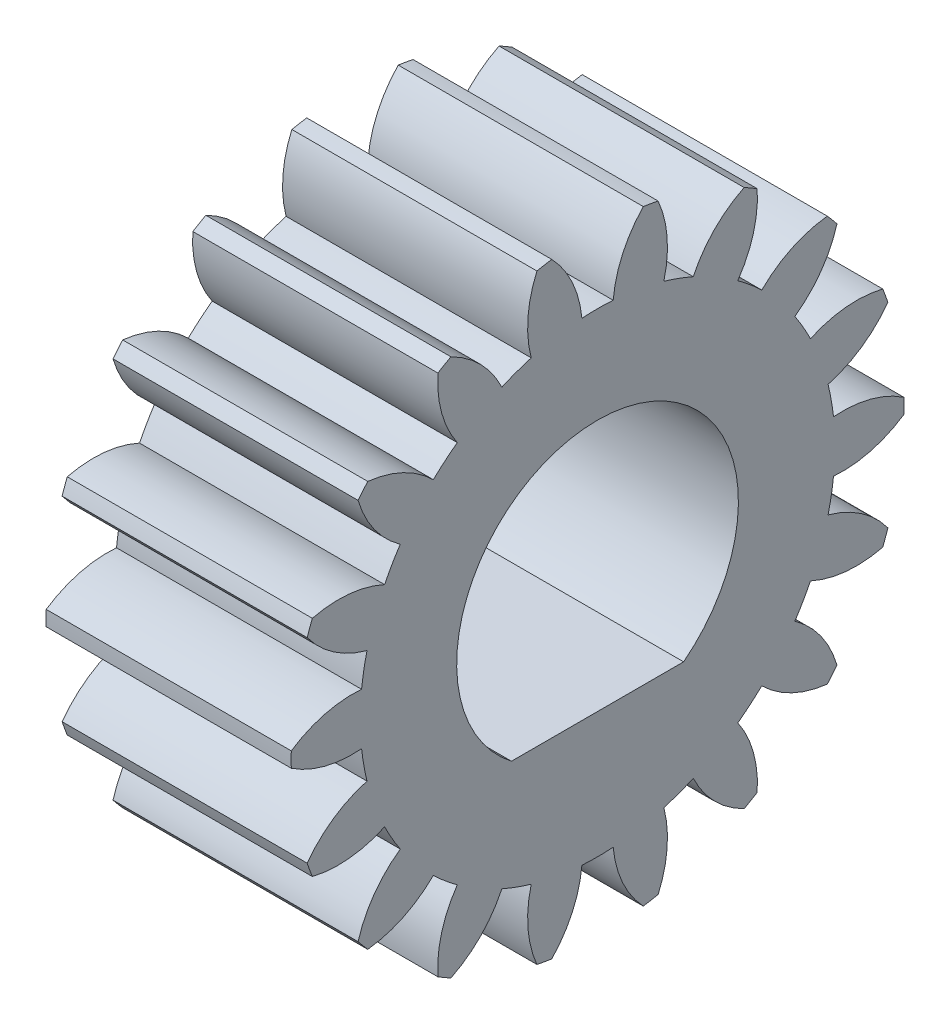
SolidWorks part; units mm, degrees
ref_plane "Plane1" through (0, 0, 0) normal (0, 0, 1) x (1, 0, 0)
ref_plane "Plane2" through (0, 0, 0) normal (0, 1, 0) x (1, 0, 0)
ref_plane "Plane3" through (0, 0, 0) normal (1, 0, 0) x (0, 0, -1)
sketch "HoldingSke" plane through (0, 0, 0) normal (0, 1, 0) x (1, 0, 0)
  line L0 (0, 0) -> (1.9021, -0.618)
  line L1 (-15, 0) -> (100, 0) construction
  line L2 (0, 0) -> (-2.1039, 2.3779)
  line L3 (0, 0) -> (-11.863, 4.5341)
  line L4 (0, 0) -> (8.2133, 2.6687)
  line L5 (0, 0) -> (-46.8476, -17.4728)
  line L6 (0, 0) -> (-3.3159, -2.2372)
  line L7 (-2.1039, 2.3779) -> (8.6586, 51.2059)
  line L8 (-76.2, 54.61) -> (-76.1, 54.61)
  line L9 (-71.009, 38.7566) -> (-53.1078, 45.2721)
  line L10 (-76.2, 71.12) -> (104.1128, 71.12)
  line L11 (0, 0) -> (-4, 0)
  line L12 (-76.2, 101.6) -> (-76.181, 101.6)
  line L13 (24.9733, 27.94) -> (52.9518, 28.4284)
  line L14 (24.9733, 27.94) -> (24.9743, 27.94)
  line L15 (24.9733, 27.94) -> (100.4006, 29.5858)
  line L16 (-63.627, -0.5) -> (-12.827, -0.5)
  circle A0 centre (0, 0) radius 0.5
  circle A1 centre (0, 0) radius 3.874
  circle A2 centre (0, 0) radius 37.5
  circle A3 centre (0, 0) radius 0.5
  dimension "MHD" = 7.748
  dimension "Hub_dia" = 75
  dimension "Bore" = 1
  dimension "MBD" = 1
  dimension "Num_teeth" = 18
  dimension "Pitch" = 2
  dimension "Overall_len" = 50
  dimension "Show_teeth" = 18
  dimension "Thickness" = 4
  dimension "OAL" = 50.0001
  dimension "T_dim" = 0.1
  dimension "Ap" = 20
  dimension "H" = 19.05
  dimension "Pitch_radius" = 180.3128
  dimension "Width" = 4
  dimension "Backlash" = 0.019
  dimension "Addendum_fac" = 1
  dimension "Dedendum_fac" = 1.25
  dimension "Clearance_fac" = 0.25
  dimension "Dedendum_add" = 0.001
  dimension "Module" = 0.5
sketch "BasProSke" plane through (0, 0, 0) normal (0, 1, 0) x (1, 0, 0)
  line L0 (-10, 0) -> (60, 0) construction
  line L1 (0, 0) -> (0, 5)
  line L2 (0, 0) -> (4, 0)
  line L3 (4, 0) -> (4, 5)
  line L4 (4, 5) -> (0, 5)
  dimension "Thickness" = 4
  dimension "Diameter" = 10
revolve "Base-Revolve" add sketch "BasProSke" angle 360 about L0
sketch "TooCutSke" plane through (0, 0, 0) normal (1, 0, 0) x (0, 0, -1)
  line L1 (0, 0) -> (0, 107) construction
  line L2 (0, 0) -> (-0.4254, 4.4798) construction
  line L3 (0, 0) -> (-1.5579, 8.835) construction
  line L4 (-0.4254, 4.4798) -> (-0.7789, 4.4175) construction
  arc A0 (0.2553, 3.8656) -> (-0.2553, 3.8656) centre (0, 0) ccw
  arc A1 (0.7686, 4.9663) -> (-0.7686, 4.9663) centre (0, 0) ccw
  circle A2 centre (0, 0) radius 4.5 construction
  circle A3 centre (0, 0) radius 4.2286 construction
  arc A4 (-0.2553, 3.8656) -> (-0.7686, 4.9663) centre (-2.0476, 3.6998) ccw
  arc A5 (0.7686, 4.9663) -> (0.2553, 3.8656) centre (2.0476, 3.6998) ccw
  dimension "Root_dia" = 7.748
  dimension "Overcut_dia" = 10.0508
  dimension "Pitch_dia" = 9
  dimension "Base_dia" = 8.4572
  dimension "Flank_rad" = 1.8
  dimension "Half_ang" = 10
  dimension "Half_CT" = 0.359
extrude "ToothCut" cut sketch "TooCutSke" along normal through all
fillet "Breaks" [suppressed] radius 0.01
fillet "RootFillets" [suppressed] radius 0.126
pattern_circular "TeethCuts" count 18 every 20 about axis through (-10, 0, 0) along (1, 0, 0) of "ToothCut", "RootFillets", "Breaks"
sketch "HubNeaOneSke" plane through (0, 0, 0) normal (-1, 0, 0) x (0, 0, 1)
  circle A0 centre (0, 0) radius 3.874
  dimension "Diameter" = 7.748
extrude "HubNearOne" [suppressed] add sketch "HubNeaOneSke" along normal blind 46.0001
sketch "HubNeaBotSke" plane through (0, 0, 0) normal (-1, 0, 0) x (0, 0, 1)
  circle A0 centre (0, 0) radius 3.874
  dimension "Diameter" = 7.748
extrude "HubNearBoth" [suppressed] add sketch "HubNeaBotSke" along normal blind 23
ref_plane "FarPln" through (4, 0, 0) normal (1, 0, 0) x (0, 0, -1)
sketch "HubFarSke" plane through (4, 0, 0) normal (1, 0, 0) x (0, 0, -1)
  circle A0 centre (0, 0) radius 3.874
  dimension "Diameter" = 7.748
extrude "HubFar" [suppressed] add sketch "HubFarSke" along normal blind 23
sketch "BorSke" plane through (0, 0, 0) normal (1, 0, 0) x (0, 0, -1)
  line L0 (-1.4048, -1.82) -> (1.4048, -1.82)
  line L2 (0, 0) -> (0, -1.82)
  arc A0 (-1.4048, -1.82) -> (1.4048, -1.82) centre (0, 0) cw
  point P2 (0, -1.5609)
extrude "Bore" cut sketch "BorSke" along normal mid plane 100.0001
sketch "KeySke" plane through (0, 0, 0) normal (1, 0, 0) x (0, 0, -1)
  line L0 (-0.05, 0) -> (-0.05, 0.6)
  line L1 (-0.05, 0.6) -> (0.05, 0.6)
  line L2 (0.05, 0.6) -> (0.05, 0)
  line L3 (0, 0) -> (0, 34) construction
  line L4 (-0.05, 0) -> (0.05, 0)
  dimension "Offset" = 0.6
  dimension "Width" = 0.1
extrude "Keyway" [suppressed] cut sketch "KeySke" along normal mid plane 100.0001
pattern_circular "Keyway2" [suppressed] count 2 every 90 about axis through (-10, 0, 0) along (1, 0, 0)
equation "' \"Module@HoldingSke\" = 6.35"
equation "' \"Num_teeth@HoldingSke\" = 12"
equation "' \"Ap@HoldingSke\" =  20"
equation "' \"Ap@HoldingSke\" = 20"
equation "' \"Width@HoldingSke\" = 0.5 * 25.4"
equation "' \"Hub_dia@HoldingSke\"= 1 * 25.4"
equation "' \"Hub_dia@HoldingSke\" = 1 * 25.4"
equation "' \"Overall_len@HoldingSke\" = 1.0 * 25.4"
equation "' \"Bore@HoldingSke\" = 0.75 * 25.4"
equation "' \"T_dim@HoldingSke\" = 0.1 * 25.4"
equation "' \"Width@KeySke\" = 0.25 * 25.4"
equation "' \"Show_teeth@HoldingSke\" = 13"
equation "' \"Backlash@HoldingSke\" = 0.009 * 25.4"
equation "' \"Addendum_fac@HoldingSke\" = 1.0"
equation "' \"Dedendum_fac@HoldingSke\" = 1.25"
equation "' \"Dedendum_add@HoldingSke\" = 0.00005 * 25.4"
equation "' \"Clearance_fac@HoldingSke\" = 0.25"
equation "\"Pitch@HoldingSke\" = 1 / \"Module@HoldingSke\""
equation "\"Overcut_dia@TooCutSke\" = (\"Num_teeth@HoldingSke\" + 2 * \"Addendum_fac@HoldingSke\") / \"Pitch@HoldingSke\" + 0.002 * 25.4"
equation "\"Pitch_dia@TooCutSke\" = \"Num_teeth@HoldingSke\" / \"Pitch@HoldingSke\""
equation "\"Base_dia@TooCutSke\" = \"Num_teeth@HoldingSke\" / \"Pitch@HoldingSke\" * cos((\"Ap@HoldingSke\"  * 3.14159265 / 180))"
equation "\"Root_dia@TooCutSke\" = (\"Num_teeth@HoldingSke\" + 2) / \"Pitch@HoldingSke\" - 2 * (\"Addendum_fac@HoldingSke\" + \"Dedendum_fac@HoldingSke\") / \"Pitch@HoldingSke\" - \"Dedendum_add@HoldingSke\" * 2"
equation "\"Half_ang@TooCutSke\" = 180 / \"Num_teeth@HoldingSke\""
equation "\"Half_CT@TooCutSke\" = \"Num_teeth@HoldingSke\" / \"Pitch@HoldingSke\" * sin((3.14159265 / 2 / \"Num_teeth@HoldingSke\")) / 2 - 7 * \"Backlash@HoldingSke\" / 4"
equation "\"Flank_rad@TooCutSke\" = \"Num_teeth@HoldingSke\" / \"Pitch@HoldingSke\" / 5"
equation "\"Radius@RootFillets\" = \"Clearance_fac@HoldingSke\" / \"Pitch@HoldingSke\" + \"Dedendum_add@HoldingSke\""
equation "\"Break_rad@Breaks\" = 0.02 / \"Pitch@HoldingSke\""
equation "\"Thickness@HoldingSke\" = \"Width@HoldingSke\""
equation "\"OAL@HoldingSke\" = \"Thickness@HoldingSke\""
equation "\"MHD@HoldingSke\" = (\"Num_teeth@HoldingSke\" + 2) / \"Pitch@HoldingSke\" - 2 * (\"Addendum_fac@HoldingSke\" + \"Dedendum_fac@HoldingSke\")  / \"Pitch@HoldingSke\" - \"Dedendum_add@HoldingSke\" * 2"
equation "\"MBD@HoldingSke\" = (\"Num_teeth@HoldingSke\" + 2) / \"Pitch@HoldingSke\" - 2 * (\"Addendum_fac@HoldingSke\" + \"Dedendum_fac@HoldingSke\")  / \"Pitch@HoldingSke\" - \"Dedendum_add@HoldingSke\" * 2 - 0.002 * 25.4"
equation "\"MHD@HoldingSke\" = ((sgn( \"MHD@HoldingSke\" - \"Hub_dia@HoldingSke\" )-1)*( \"MHD@HoldingSke\" - \"Hub_dia@HoldingSke\" ))/-2+ \"Hub_dia@HoldingSke\""
equation "\"MBD@HoldingSke\" = ((sgn( \"MBD@HoldingSke\" - \"Bore@HoldingSke\" )-1)*( \"MBD@HoldingSke\" - \"Bore@HoldingSke\" ))/-2+ \"Bore@HoldingSke\""
equation "\"OAL@HoldingSke\" = ((sgn( \"OAL@HoldingSke\" - \"Overall_len@HoldingSke\" )+1)*( \"OAL@HoldingSke\" - \"Overall_len@HoldingSke\" ))/2 + \"Overall_len@HoldingSke\" + 0.000002 * 25.4"
equation "\"Num_teeth@TeethCuts\" = int( \"Show_teeth@HoldingSke\" ) + 1"
equation "\"Num_teeth@TeethCuts\" = ((sgn( \"Num_teeth@TeethCuts\" - \"Num_teeth@HoldingSke\" )-1)*( \"Num_teeth@TeethCuts\" - \"Num_teeth@HoldingSke\" ))/-2+ \"Num_teeth@HoldingSke\""
equation "\"Num_teeth@TeethCuts\" = ((sgn( \"Num_teeth@TeethCuts\" - 2.0)+1)*( \"Num_teeth@TeethCuts\" - 2.0))/2 +2.0"
equation "\"Angle@TeethCuts\" = 360.0 / \"Num_teeth@HoldingSke\""
equation "\"Diameter@BasProSke\" = (\"Num_teeth@HoldingSke\" + 2 * \"Addendum_fac@HoldingSke\") / \"Pitch@HoldingSke\""
equation "\"Thickness@BasProSke\"  = \"Thickness@HoldingSke\""
equation "' \"Fillet_rad@BasProSke\" =  \"Thickness@HoldingSke\" * 0.05"
equation "' \"Fillet_rad@BasProSke\" = \"Thickness@HoldingSke\" * 0.05"
equation "\"MHD@HoldingSke\" = ((sgn( \"MHD@HoldingSke\" - \"Root_dia@TooCutSke\" )-1)*( \"MHD@HoldingSke\" - \"Root_dia@TooCutSke\" ))/-2+ \"Root_dia@TooCutSke\""
equation "\"Diameter@HubNeaOneSke\" = \"MHD@HoldingSke\""
equation "\"Length@HubNearOne\" = \"OAL@HoldingSke\" - \"Thickness@BasProSke\""
equation "\"Diameter@HubNeaBotSke\" = \"MHD@HoldingSke\""
equation "\"Length@HubNearBoth\" = ( \"OAL@HoldingSke\" - \"Thickness@BasProSke\" ) / 2.0"
equation "\"Thickness@FarPln\" = \"Thickness@BasProSke\""
equation "\"Diameter@HubFarSke\" = \"MHD@HoldingSke\""
equation "\"Length@HubFar\" = ( \"OAL@HoldingSke\" - \"Thickness@BasProSke\" ) / 2.0"
equation "\"D1@Bore\" = \"OAL@HoldingSke\" * 2.0"
equation "\"D1@Keyway\" = \"OAL@HoldingSke\" * 2.0"
equation "\"Offset@KeySke\" = \"T_dim@HoldingSke\" + \"MBD@HoldingSke\" / 2.0"
